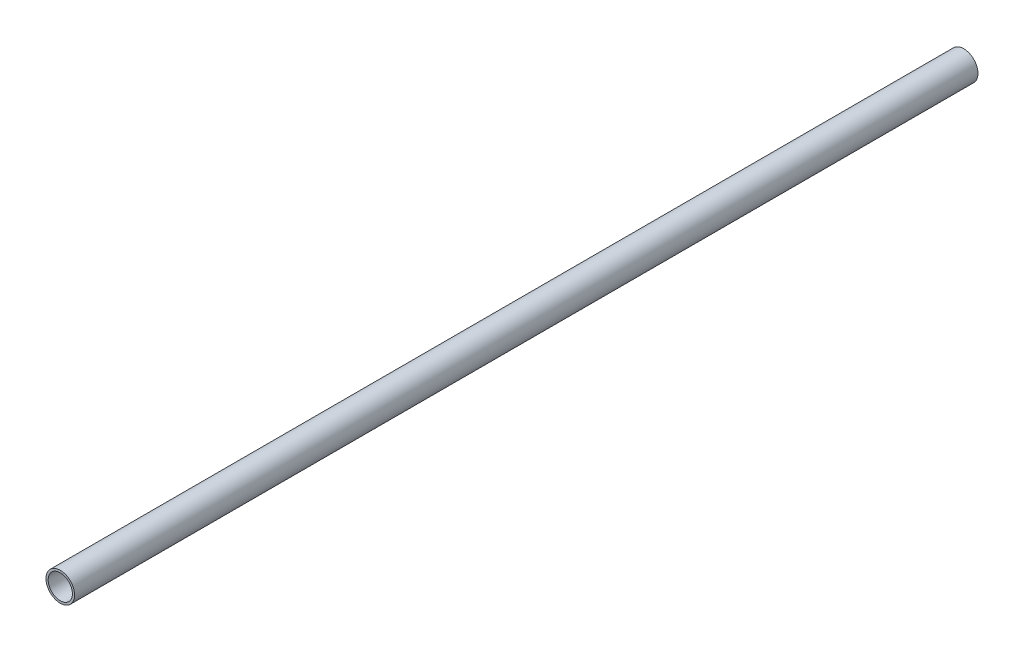
SolidWorks part; units mm, degrees
ref_plane "Front Plane" through (0, 0, 0) normal (0, 0, 1) x (1, 0, 0)
ref_plane "Top Plane" through (0, 0, 0) normal (0, 1, 0) x (1, 0, 0)
ref_plane "Right Plane" through (0, 0, 0) normal (1, 0, 0) x (0, 0, -1)
sketch "Sketch2" plane through (0, 0, 0) normal (1, 0, 0) x (0, 0, -1)
  line L0 (-698.5, 24.13) -> (-698.5, -24.13) construction
  line L1 (762, -24.13) -> (-762, -24.13)
  line L2 (762, -24.13) -> (762, 24.13)
  line L3 (762, 24.13) -> (-762, 24.13)
  line L4 (-762, -24.13) -> (-762, 24.13)
  line L5 (762, -24.13) -> (-762, 24.13) construction
  line L6 (762, 24.13) -> (-762, -24.13) construction
  line L7 (698.5, 24.13) -> (698.5, -24.13) construction
  point P0 (0, 0)
  point P6 (-762, 20.447)
  point P11 (-762, -20.447)
  dimension "Rail OD" = 48.26
  dimension "Wall Thickness" = 3.683
  dimension "Length" = 1524
  dimension "D1" = 63.5
  dimension "D2" = 63.5
  dimension "D3" = 3.683
sketch "Sketch1" plane through (0, 0, 0) normal (0, 0, 1) x (1, 0, 0)
  line L0 (24.13, 0) -> (20.447, 0) construction
  circle A0 centre (0, 0) radius 24.13
  dimension "D1" = 3.683
extrude "Extrude-Thin1" add sketch "Sketch1" along normal mid plane 1524 thin thin type one direction reverse wall 3.683
equation "\"D1@Sketch1\"=\"Wall Thickness@Sketch2\""
equation "\"D5@Extrude-Thin1\" = \"Wall Thickness@Sketch2\""
equation "\"D1@Extrude-Thin1\" = \"Length@Sketch2\""
equation "\"D2@Sketch2\"=\"D1@Sketch2\""
equation "\"D3@Sketch2\"= \"Wall Thickness@Sketch2\""
